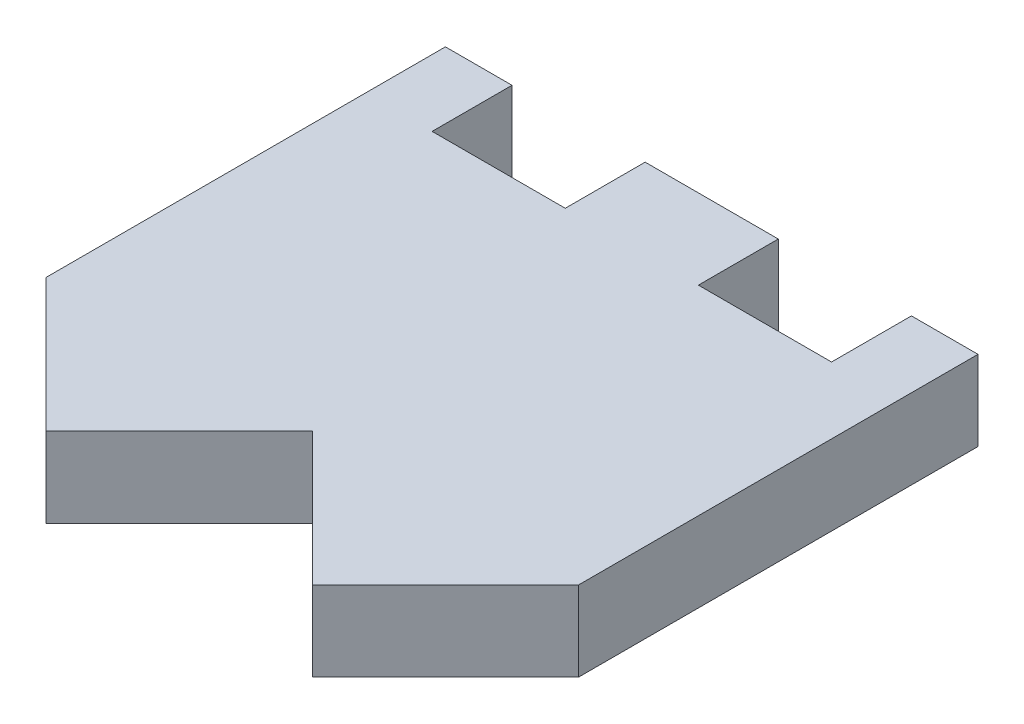
SolidWorks part; units mm, degrees
ref_plane "Front Plane" through (0, 0, 0) normal (0, 0, 1) x (1, 0, 0)
ref_plane "Top Plane" through (0, 0, 0) normal (0, 1, 0) x (1, 0, 0)
ref_plane "Right Plane" through (0, 0, 0) normal (1, 0, 0) x (0, 0, -1)
sketch "Sketch1" plane through (0, 0, 0) normal (0, 1, 0) x (1, 0, 0)
  line L1 (-10, -10) -> (10, -10)
  line L2 (-10, -10) -> (-10, 10)
  line L3 (-10, 10) -> (10, 10)
  line L4 (10, -10) -> (10, 10)
  line L5 (-10, -10) -> (10, 10) construction
  line L6 (-10, 10) -> (10, -10) construction
  point P0 (0, 0)
  dimension "D1" = 20
  dimension "D2" = 20
extrude "Boss-Extrude1" add sketch "Sketch1" along normal blind 3
sketch "Sketch2" plane through (0, 3, 0) normal (0, 1, 0) x (1, 0, 0)
  line L0 (-10, -5) -> (-5, -10)
  line L1 (-10, 10) -> (-10, -10) construction
  line L2 (-10, -10) -> (10, -10) construction
  line L3 (-5, -10) -> (0, -5)
  line L4 (0, -5) -> (5, -10)
  line L5 (5, -10) -> (10, -5)
  line L6 (10, -10) -> (10, 10) construction
  line L7 (10, -5) -> (10, -10)
  line L8 (10, -10) -> (-10, -10)
  line L9 (-10, -10) -> (-10, -5)
  point P6 (0, 0)
  point P17 (0.7828, -3.8034)
  line M1 (10, -10) -> (10, 10)
  line M3 (-10, 10) -> (-10, -10)
  line M4 (-10, -10) -> (10, -10)
  dimension "D1" = 5
  dimension "D2" = 5
  dimension "D3" = 5
extrude "Cut-Extrude1" cut sketch "Sketch2" against normal through all both and the other way through all contours L0 M3 M4 | L4 L3 M4 | L5 M4 M1
sketch "Sketch3" plane through (0, 3, 0) normal (0, 1, 0) x (1, 0, 0)
  line L0 (10, 10) -> (-10, 10) construction
  line L1 (-7.5, 10) -> (-2.5, 10)
  line L2 (-7.5, 10) -> (-7.5, 7)
  line L3 (-7.5, 7) -> (-2.5, 7)
  line L4 (-2.5, 10) -> (-2.5, 7)
  line L5 (-10, 10) -> (-10, -5) construction
  dimension "D1" = 3
  dimension "D2" = 5
  dimension "D3" = 2.5
extrude "Cut-Extrude2" cut sketch "Sketch3" against normal through all both and the other way through all
mirror "Mirror1" about plane through (0, 0, 0) normal (1, 0, 0) of "Cut-Extrude2"
